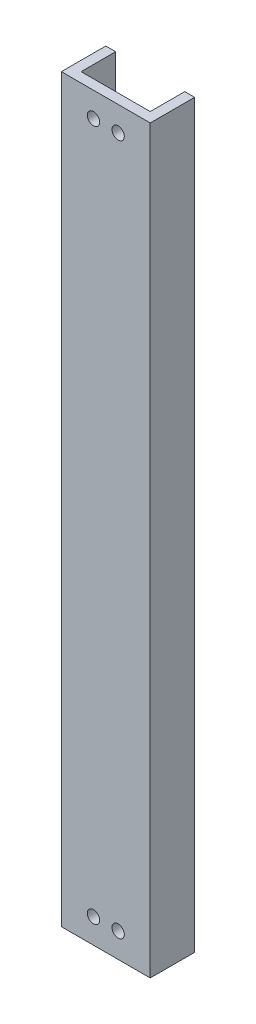
SolidWorks part; units mm, degrees
ref_plane "Front Plane" through (0, 0, 0) normal (0, 0, 1) x (1, 0, 0)
ref_plane "Top Plane" through (0, 0, 0) normal (0, 1, 0) x (1, 0, 0)
ref_plane "Right Plane" through (0, 0, 0) normal (1, 0, 0) x (0, 0, -1)
sketch "Sketch1" plane through (0, 0, 0) normal (0, 1, 0) x (1, 0, 0)
  line L0 (-7, 4.5) -> (-7, -2.5)
  line L2 (-9, 4.5) -> (-9, -4.5)
  line L3 (-9, -4.5) -> (9, -4.5)
  line L4 (9, 4.5) -> (9, -4.5)
  line L5 (-9, 4.5) -> (9, -4.5) construction
  line L6 (-9, -4.5) -> (9, 4.5) construction
  line L7 (-7, -2.5) -> (7, -2.5)
  line L8 (7, 4.5) -> (7, -2.5)
  line L9 (-9, 4.5) -> (-7, 4.5)
  line L10 (9, 4.5) -> (7, 4.5)
  point P0 (0, 0)
  dimension "D1" = 18
  dimension "D2" = 9
  dimension "D4" = 14
  dimension "D5" = 9
  dimension "D3" = 2
extrude "Boss-Extrude1" add sketch "Sketch1" along normal blind 150
sketch "Sketch2" plane through (0, 0, 2.5) normal (0, 0, -1) x (-1, 0, 0)
  line L0 (0, 150) -> (0, 0) construction
  line L1 (-7, 150) -> (7, 150) construction
  line L2 (-7, 2) -> (7, 2) construction
  line L3 (-7, 150) -> (-7, 0) construction
  line L4 (7, 150) -> (7, 0) construction
  line L5 (-7, 0) -> (7, 0) construction
  line L6 (-9, 75) -> (9, 75) construction
  line L7 (-9, 150) -> (-9, 0) construction
  line L8 (9, 150) -> (9, 0) construction
  circle A0 centre (-2.5, 5) radius 1.25
  circle A1 centre (2.5, 5) radius 1.25
  circle A2 centre (2.5, 145) radius 1.25
  circle A3 centre (-2.5, 145) radius 1.25
  dimension "D2" = 2.5
  dimension "D3" = 2.5
  dimension "D1" = 2
  dimension "D4" = 5
  dimension "D5" = 2.5
  dimension "D6" = 3
  dimension "D7" = 3
extrude "Cut-Extrude1" cut sketch "Sketch2" against normal blind 10
